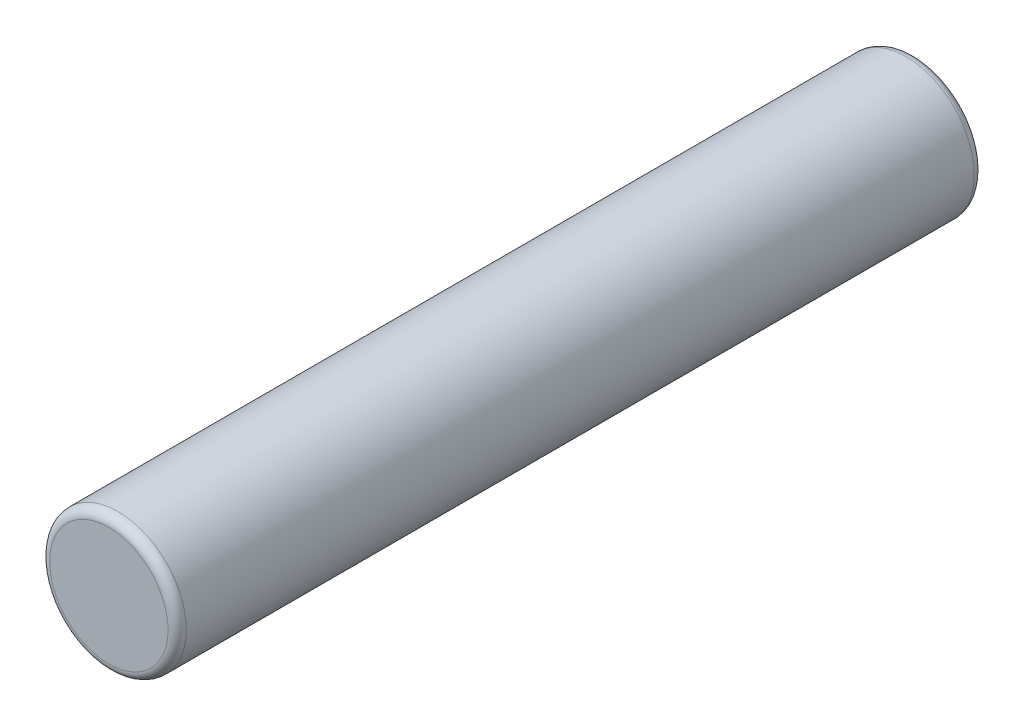
SolidWorks part; units mm, degrees
ref_plane "Front Plane" through (0, 0, 0) normal (0, 0, 1) x (1, 0, 0)
ref_plane "Top Plane" through (0, 0, 0) normal (0, 1, 0) x (1, 0, 0)
ref_plane "Right Plane" through (0, 0, 0) normal (1, 0, 0) x (0, 0, -1)
sketch "Sketch1" plane through (0, 0, 0) normal (0, 0, 1) x (1, 0, 0)
  circle A0 centre (0, 0) radius 1.5
  dimension "D1" = 3
extrude "Boss-Extrude1" add sketch "Sketch1" along normal blind 17.7
fillet "Fillet1" radius 0.2 2 edges at (1.5, 0, 0) (1.5, 0, 17.7)
